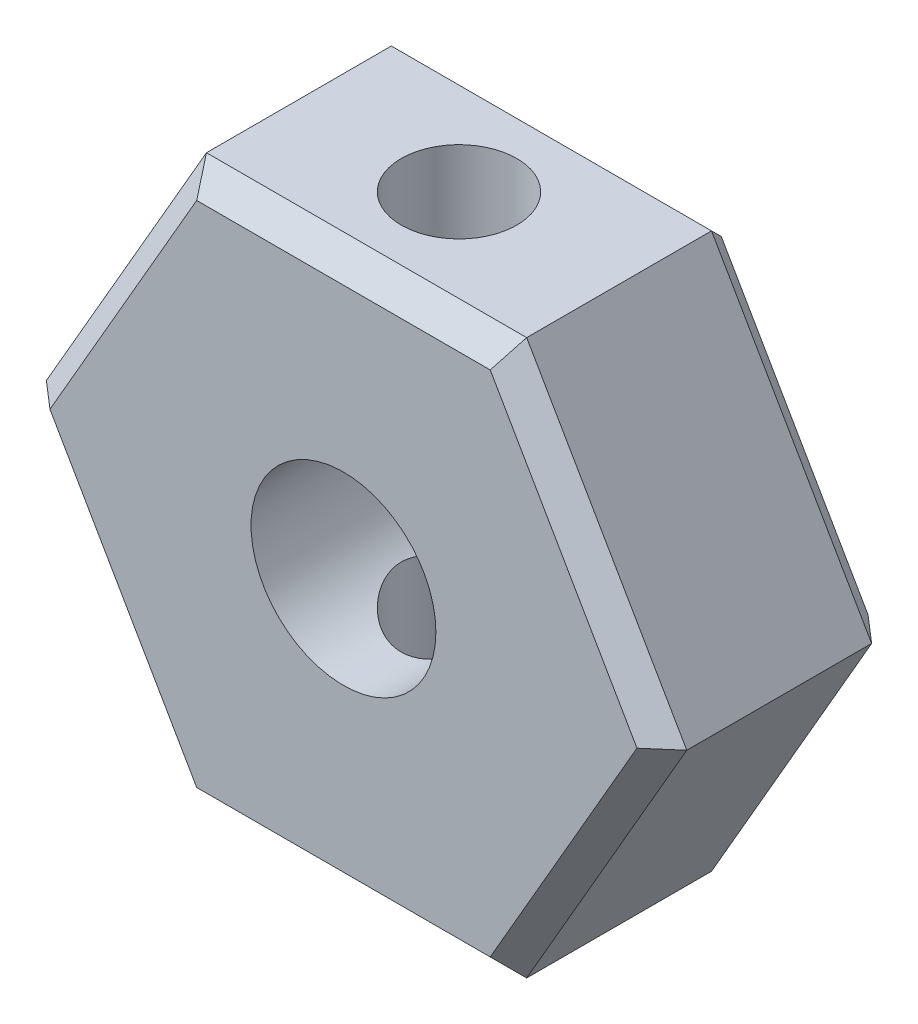
SolidWorks part; units mm, degrees
ref_plane "Alzado" through (0, 0, 0) normal (0, 0, 1) x (1, 0, 0)
ref_plane "Planta" through (0, 0, 0) normal (0, 1, 0) x (1, 0, 0)
ref_plane "Vista lateral" through (0, 0, 0) normal (1, 0, 0) x (0, 0, -1)
sketch "Croquis1" plane through (0, 0, 0) normal (0, 0, 1) x (1, 0, 0)
  line L1 (6.9282, 0) -> (3.4641, 6)
  line L2 (3.4641, 6) -> (-3.4641, 6)
  line L3 (-3.4641, 6) -> (-6.9282, 0)
  line L4 (-6.9282, 0) -> (-3.4641, -6)
  line L5 (-3.4641, -6) -> (3.4641, -6)
  line L6 (3.4641, -6) -> (6.9282, 0)
  circle A0 centre (0, 0) radius 6 construction
extrude "Saliente-Extruir1" add sketch "Croquis1" along normal blind 5
sketch "Croquis2" plane through (0, 0, 5) normal (0, 0, 1) x (1, 0, 0)
  circle A0 centre (0, 0) radius 2
extrude "Cortar-Extruir1" cut sketch "Croquis2" against normal blind 5
chamfer "Chaflán1" distance 0.5 angle 45 12 edges at (5.1962, 3, 0) (0, 6, 0) (-5.1962, 3, 0) (-5.1962, -3, 0) (0, -6, 0) (5.1962, -3, 0) (0, -6, 5) (-5.1962, -3, 5) (-5.1962, 3, 5) (0, 6, 5) (5.1962, 3, 5) (5.1962, -3, 5)
sketch "Croquis3" plane through (0, 6, 0) normal (0, 1, 0) x (1, 0, 0)
  circle A0 centre (0, -2.5) radius 1.25
extrude "Cortar-Extruir2" cut sketch "Croquis3" against normal through all
